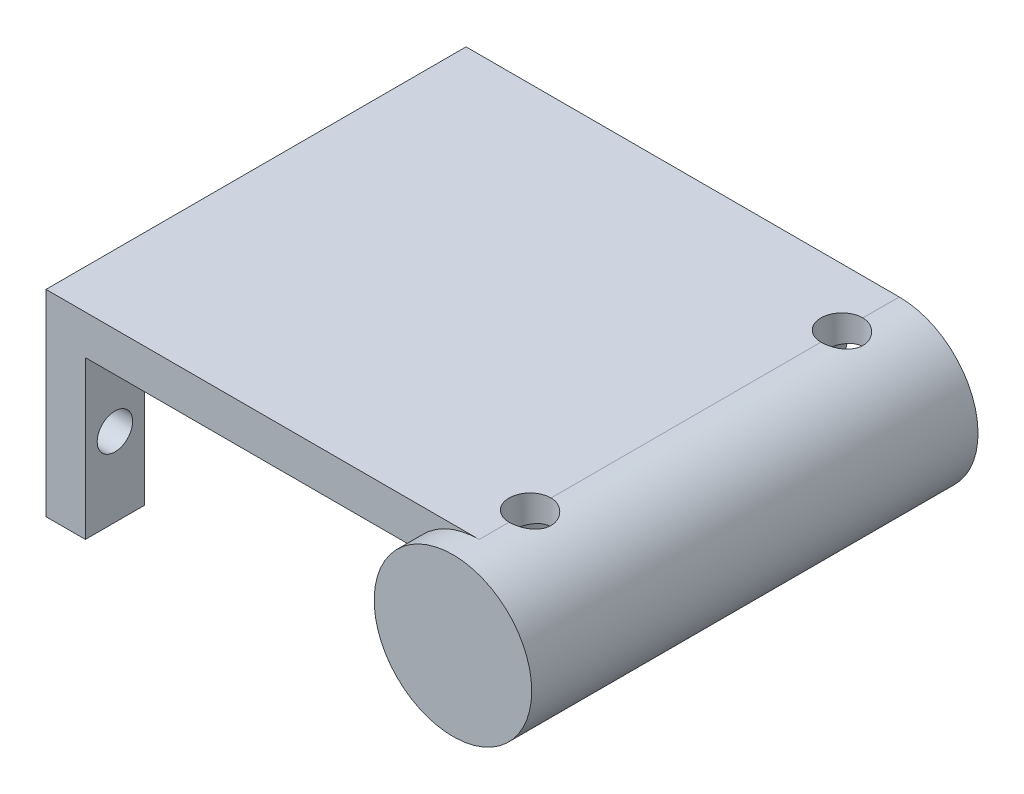
SolidWorks part; units mm, degrees
ref_plane "前视基准面" through (0, 0, 0) normal (0, 0, 1) x (1, 0, 0)
ref_plane "上视基准面" through (0, 0, 0) normal (0, 1, 0) x (1, 0, 0)
ref_plane "右视基准面" through (0, 0, 0) normal (1, 0, 0) x (0, 0, -1)
other "Configuration Table"
sketch "草图1" plane through (0, 0, 0) normal (0, 0, 1) x (1, 0, 0)
  line L0 (-32.4058, 8.6736) -> (-5.4058, 8.6736)
  line L1 (-4.6019, 5.6736) -> (-29.4058, 5.6736)
  line L2 (-5.4058, 8.6736) -> (-5.4058, 5.6736) construction
  line L3 (-32.4058, 5.6736) -> (-32.4058, 8.6736)
  line L4 (-5.4058, 8.6736) -> (0.5942, 8.6736)
  line L7 (-32.4058, 5.6736) -> (-32.4058, -6.3264)
  line L8 (-32.4058, -6.3264) -> (-29.4058, -6.3264)
  line L9 (-29.4058, 5.6736) -> (-29.4058, -6.3264)
  arc A0 (-4.6019, 5.6736) -> (0.5942, 8.6736) centre (0.5942, 2.6736) ccw
  circle A1 centre (0.5942, 2.6736) radius 4.1
  dimension "D1" = 12
  dimension "D2" = 8.2
  dimension "D3" = 3
  dimension "D4" = 27
  dimension "D5" = 3
  dimension "D6" = 12
extrude "凸台-拉伸1" add sketch "草图1" along normal blind 32
sketch "草图3" plane through (-32.4058, 0, 0) normal (-1, 0, 0) x (0, 0, 1)
  line L0 (0, 8.6736) -> (0, -6.3264) construction
  line L1 (32, -6.3264) -> (0, -6.3264) construction
  line L2 (32, -6.3264) -> (32, 5.6736) construction
  line L3 (32, 5.6736) -> (0, 5.6736) construction
  line L4 (0, -6.3264) -> (0, 5.6736) construction
  line L5 (32, 8.6736) -> (0, 8.6736) construction
  line L6 (27.5, 5.6736) -> (27.5, -6.3264)
  line L7 (4.5, 5.6736) -> (4.5, -6.3264)
  line L8 (27.5, -0.3264) -> (4.5, -0.3264) construction
  line L9 (16, 5.6736) -> (16, -6.3264) construction
  line L10 (27.5, 5.6736) -> (4.5, 5.6736)
  line L11 (4.5, -6.3264) -> (27.5, -6.3264)
  line L12 (27.5, -0.3264) -> (32, -0.3264) construction
  line L13 (4.5, -0.3264) -> (0, -0.3264) construction
  circle A0 centre (29.75, -0.3264) radius 1.35
  circle A1 centre (2.25, -0.3264) radius 1.35
  point P15 (16, -0.3264)
  dimension "D3" = 2.7
  dimension "D1" = 3
  dimension "D2" = 23
extrude "切除-拉伸1" cut sketch "草图3" against normal blind 5 contours L11 L6 L10 L7 | A0 | A1
sketch "草图4" plane through (0, 0, 0) normal (0, 1, 0) x (1, 0, 0)
  line L0 (0.5942, -32) -> (0.5942, 0) construction
  line L1 (-5.4058, -32) -> (6.5942, -32) construction
  circle A0 centre (0.5942, -4.3653) radius 1.6
  circle A1 centre (0.5942, -28.1239) radius 1.6
  dimension "D1" = 3.2
extrude "切除-拉伸2" cut sketch "草图4" against normal mid plane 20
sketch "草图5" plane through (0, 0, 32) normal (0, 0, 1) x (1, 0, 0)
  circle A0 centre (0.5942, 2.6736) radius 6
extrude "凸台-拉伸2" add sketch "草图5" along normal blind 2
